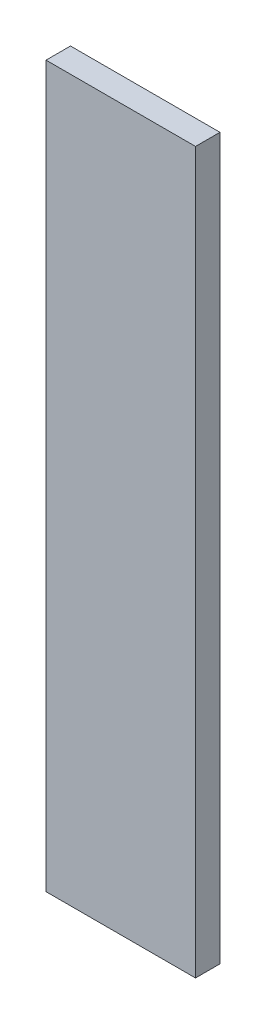
SolidWorks part; units mm, degrees
material "Balsa"
ref_plane "Front Plane" through (0, 0, 0) normal (0, 0, 1) x (1, 0, 0)
ref_plane "Top Plane" through (0, 0, 0) normal (0, 1, 0) x (1, 0, 0)
ref_plane "Right Plane" through (0, 0, 0) normal (1, 0, 0) x (0, 0, -1)
sketch "Sketch1" plane through (0, 0, 0) normal (0, 0, 1) x (1, 0, 0)
  line L1 (-55, 265) -> (55, 265)
  line L2 (-55, 265) -> (-55, -265)
  line L3 (-55, -265) -> (55, -265)
  line L4 (55, 265) -> (55, -265)
  line L5 (-55, 265) -> (55, -265) construction
  line L6 (-55, -265) -> (55, 265) construction
  point P0 (0, 0)
  dimension "D1" = 110
  dimension "D2" = 530
extrude "Boss-Extrude1" add sketch "Sketch1" along normal blind 18
